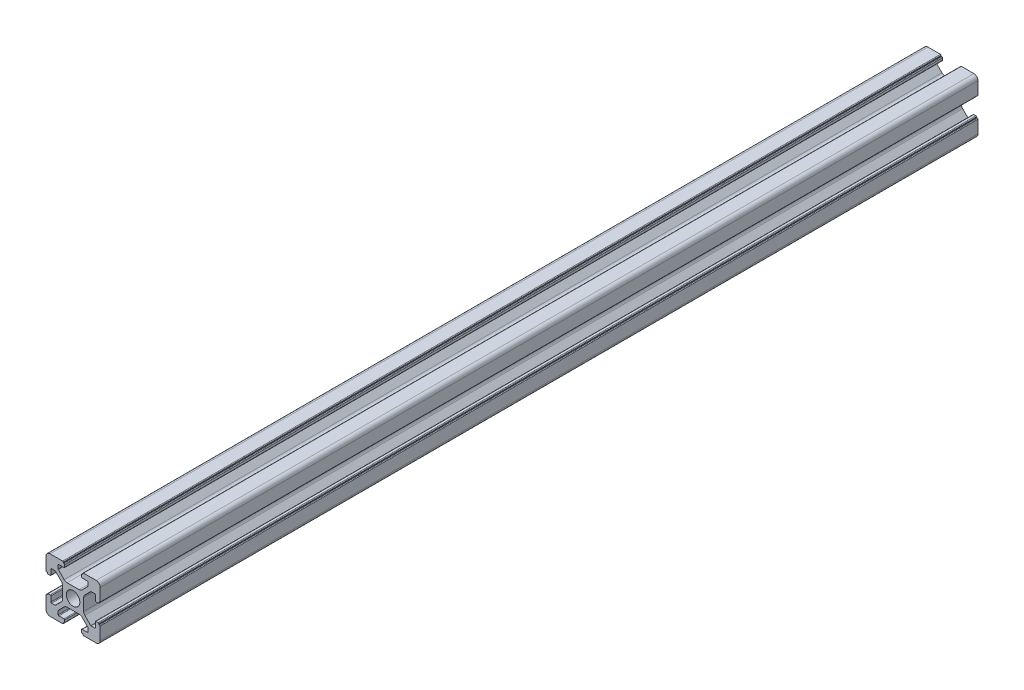
SolidWorks part; units mm, degrees
material "1060 Alloy"
ref_plane "前视基准面" through (0, 0, 0) normal (0, 0, 1) x (1, 0, 0)
ref_plane "上视基准面" through (0, 0, 0) normal (0, 1, 0) x (1, 0, 0)
ref_plane "右视基准面" through (0, 0, 0) normal (1, 0, 0) x (0, 0, -1)
sketch "草图1" plane through (0, 0, 0) normal (0, 0, 1) x (1, 0, 0)
  line L0 (0, 0) -> (0, 5.5) construction
  line L1 (-8.5023, -10.0023) -> (-3.85, -10.0023)
  line L2 (-10.0023, -8.5023) -> (-10.0023, -3.85)
  line L3 (-8.5023, 10.0023) -> (-3.85, 10.0023)
  line L4 (10.0023, -8.5023) -> (10.0023, -3.85)
  line L5 (-10.0023, -10.0023) -> (10.0023, 10.0023) construction
  line L6 (-10.0023, 10.0023) -> (10.0023, -10.0023) construction
  line L7 (-2.218, -3.9) -> (2.218, -3.9)
  line L8 (-3.9, -2.218) -> (-3.9, 2.218)
  line L9 (-2.218, 3.9) -> (2.218, 3.9)
  line L10 (3.9, -2.218) -> (3.9, 2.218)
  line L11 (-3.9, -3.9) -> (3.9, 3.9) construction
  line L12 (-3.9, 3.9) -> (3.9, -3.9) construction
  line L13 (-5.25, -8.2) -> (-3.35, -8.2)
  line L14 (-8.2, -5.25) -> (-8.2, -3.35)
  line L15 (-5.25, 8.2) -> (-3.35, 8.2)
  line L16 (8.2, -5.25) -> (8.2, -3.35)
  line L17 (-8.2, -8.2) -> (8.2, 8.2) construction
  line L18 (-8.2, 8.2) -> (8.2, -8.2) construction
  line L19 (-7.95, 5.5) -> (-6.6642, 5.5)
  line L20 (0, 0) -> (5.5, 0) construction
  line L23 (-5.5, 7.95) -> (-5.5, 6.6642)
  line L26 (0, 0) -> (-0.5303, 0.5303)
  line L27 (3.2787, 4.3393) -> (5.4268, 6.4874)
  line L28 (0, 0) -> (0.5303, -0.5303)
  line L29 (5.5, 6.6642) -> (5.5, 7.95)
  line L30 (4.3393, 3.2787) -> (6.4874, 5.4268)
  line L31 (6.6642, 5.5) -> (7.95, 5.5)
  line L32 (4.3393, -3.2787) -> (6.4874, -5.4268)
  line L33 (3.2787, -4.3393) -> (5.4268, -6.4874)
  line L34 (-3.2787, -4.3393) -> (-5.4268, -6.4874)
  line L35 (-4.3393, -3.2787) -> (-6.4874, -5.4268)
  line L36 (-4.3393, 3.2787) -> (-6.4874, 5.4268)
  line L37 (-3.2787, 4.3393) -> (-5.4268, 6.4874)
  line L38 (3.1, -8.45) -> (3.1, -9.2523)
  line L39 (8.45, 3.1) -> (9.2523, 3.1)
  line L40 (-5.5, -6.6642) -> (-5.5, -7.95)
  line L41 (-6.6642, -5.5) -> (-7.95, -5.5)
  line L42 (5.5, -6.6642) -> (5.5, -7.95)
  line L43 (6.6642, -5.5) -> (7.95, -5.5)
  line L44 (9.2523, -3.1) -> (8.45, -3.1)
  line L46 (10.0023, 3.85) -> (10.0023, 8.5023)
  line L47 (8.2, 3.35) -> (8.2, 5.25)
  line L48 (-3.1, -9.2523) -> (-3.1, -8.45)
  line L49 (-8.45, -3.1) -> (-9.2523, -3.1)
  line L50 (-9.2523, 3.1) -> (-8.45, 3.1)
  line L51 (-3.1, 8.45) -> (-3.1, 9.2523)
  line L52 (3.1, 9.2523) -> (3.1, 8.45)
  line L53 (3.85, 10.0023) -> (8.5023, 10.0023)
  line L54 (3.35, 8.2) -> (5.25, 8.2)
  line L55 (-10.0023, 3.85) -> (-10.0023, 8.5023)
  line L56 (-8.2, 3.35) -> (-8.2, 5.25)
  line L57 (3.35, -8.2) -> (5.25, -8.2)
  line L58 (3.85, -10.0023) -> (8.5023, -10.0023)
  line L59 (9.7523, -3.6) -> (9.5023, -3.6)
  line L61 (9.7523, 3.6) -> (9.5023, 3.6)
  line L62 (9.5023, -3.6) -> (9.5023, -3.35)
  line L63 (3.6, -9.7523) -> (3.6, -9.5023)
  line L64 (3.35, -9.5023) -> (3.6, -9.5023)
  line L65 (9.5023, 3.35) -> (9.5023, 3.6)
  line L66 (-3.6, -9.5023) -> (-3.35, -9.5023)
  line L67 (-3.6, -9.7523) -> (-3.6, -9.5023)
  line L68 (-9.7523, -3.6) -> (-9.5023, -3.6)
  line L69 (-9.5023, -3.35) -> (-9.5023, -3.6)
  line L70 (-9.5023, 3.6) -> (-9.5023, 3.35)
  line L71 (-9.7523, 3.6) -> (-9.5023, 3.6)
  line L72 (-3.6, 9.7523) -> (-3.6, 9.5023)
  line L73 (-3.35, 9.5023) -> (-3.6, 9.5023)
  line L74 (3.6, 9.5023) -> (3.35, 9.5023)
  line L75 (3.6, 9.7523) -> (3.6, 9.5023)
  circle A0 centre (0, 0) radius 2.5
  arc A1 (10.0023, 8.5023) -> (8.5023, 10.0023) centre (8.5023, 8.5023) ccw
  arc A2 (8.5023, -10.0023) -> (10.0023, -8.5023) centre (8.5023, -8.5023) ccw
  arc A3 (-10.0023, -8.5023) -> (-8.5023, -10.0023) centre (-8.5023, -8.5023) ccw
  arc A4 (-10.0023, 8.5023) -> (-8.5023, 10.0023) centre (-8.5023, 8.5023) cw
  arc A5 (-9.5023, -3.35) -> (-9.2523, -3.1) centre (-9.2523, -3.35) cw
  arc A6 (-9.7523, -3.6) -> (-10.0023, -3.85) centre (-9.7523, -3.85) ccw
  arc A7 (-8.45, -3.1) -> (-8.2, -3.35) centre (-8.45, -3.35) cw
  arc A8 (-7.95, -5.5) -> (-8.2, -5.25) centre (-7.95, -5.25) cw
  arc A9 (-6.4874, -5.4268) -> (-6.6642, -5.5) centre (-6.6642, -5.25) cw
  arc A10 (-5.4268, -6.4874) -> (-5.5, -6.6642) centre (-5.25, -6.6642) ccw
  arc A11 (-5.5, -7.95) -> (-5.25, -8.2) centre (-5.25, -7.95) ccw
  arc A12 (-3.6, -9.7523) -> (-3.85, -10.0023) centre (-3.85, -9.7523) cw
  arc A13 (-3.35, -9.5023) -> (-3.1, -9.2523) centre (-3.35, -9.2523) ccw
  arc A14 (-3.1, -8.45) -> (-3.35, -8.2) centre (-3.35, -8.45) ccw
  arc A15 (3.1, -8.45) -> (3.35, -8.2) centre (3.35, -8.45) cw
  arc A16 (5.5, -7.95) -> (5.25, -8.2) centre (5.25, -7.95) cw
  arc A17 (5.4268, -6.4874) -> (5.5, -6.6642) centre (5.25, -6.6642) cw
  arc A18 (6.4874, -5.4268) -> (6.6642, -5.5) centre (6.6642, -5.25) ccw
  arc A19 (7.95, -5.5) -> (8.2, -5.25) centre (7.95, -5.25) ccw
  arc A20 (8.45, -3.1) -> (8.2, -3.35) centre (8.45, -3.35) ccw
  arc A21 (9.5023, -3.35) -> (9.2523, -3.1) centre (9.2523, -3.35) ccw
  arc A22 (9.7523, -3.6) -> (10.0023, -3.85) centre (9.7523, -3.85) cw
  arc A23 (3.35, -9.5023) -> (3.1, -9.2523) centre (3.35, -9.2523) cw
  arc A24 (3.6, -9.7523) -> (3.85, -10.0023) centre (3.85, -9.7523) ccw
  arc A25 (7.95, 5.5) -> (8.2, 5.25) centre (7.95, 5.25) cw
  arc A26 (8.2, 3.35) -> (8.45, 3.1) centre (8.45, 3.35) ccw
  arc A27 (9.5023, 3.35) -> (9.2523, 3.1) centre (9.2523, 3.35) cw
  arc A28 (9.7523, 3.6) -> (10.0023, 3.85) centre (9.7523, 3.85) ccw
  arc A29 (6.6642, 5.5) -> (6.4874, 5.4268) centre (6.6642, 5.25) ccw
  arc A30 (5.4268, 6.4874) -> (5.5, 6.6642) centre (5.25, 6.6642) ccw
  arc A31 (5.5, 7.95) -> (5.25, 8.2) centre (5.25, 7.95) ccw
  arc A32 (3.1, 8.45) -> (3.35, 8.2) centre (3.35, 8.45) ccw
  arc A33 (3.6, 9.7523) -> (3.85, 10.0023) centre (3.85, 9.7523) cw
  arc A34 (3.35, 9.5023) -> (3.1, 9.2523) centre (3.35, 9.2523) ccw
  arc A35 (-9.7523, 3.6) -> (-10.0023, 3.85) centre (-9.7523, 3.85) cw
  arc A36 (-9.5023, 3.35) -> (-9.2523, 3.1) centre (-9.2523, 3.35) ccw
  arc A37 (-8.45, 3.1) -> (-8.2, 3.35) centre (-8.45, 3.35) ccw
  arc A38 (-8.2, 5.25) -> (-7.95, 5.5) centre (-7.95, 5.25) cw
  arc A39 (-6.4874, 5.4268) -> (-6.6642, 5.5) centre (-6.6642, 5.25) ccw
  arc A40 (-5.4268, 6.4874) -> (-5.5, 6.6642) centre (-5.25, 6.6642) cw
  arc A41 (-5.5, 7.95) -> (-5.25, 8.2) centre (-5.25, 7.95) cw
  arc A42 (-3.1, 8.45) -> (-3.35, 8.2) centre (-3.35, 8.45) cw
  arc A43 (-3.1, 9.2523) -> (-3.35, 9.5023) centre (-3.35, 9.2523) ccw
  arc A44 (-3.6, 9.7523) -> (-3.85, 10.0023) centre (-3.85, 9.7523) ccw
  arc A45 (-4.3393, 3.2787) -> (-3.9, 2.218) centre (-5.4, 2.218) cw
  arc A46 (-3.2787, 4.3393) -> (-2.218, 3.9) centre (-2.218, 5.4) ccw
  arc A47 (3.2787, 4.3393) -> (2.218, 3.9) centre (2.218, 5.4) cw
  arc A48 (4.3393, 3.2787) -> (3.9, 2.218) centre (5.4, 2.218) ccw
  arc A49 (4.3393, -3.2787) -> (3.9, -2.218) centre (5.4, -2.218) cw
  arc A50 (3.2787, -4.3393) -> (2.218, -3.9) centre (2.218, -5.4) ccw
  arc A51 (-4.3393, -3.2787) -> (-3.9, -2.218) centre (-5.4, -2.218) ccw
  arc A52 (-2.218, -3.9) -> (-3.2787, -4.3393) centre (-2.218, -5.4) ccw
  point P0 (0, 0)
  point P7 (10.0023, 0)
  point P62 (0, 0)
  point P76 (0, 0)
  point P92 (-8.2, -5.5)
  point P99 (0, 0)
  point P106 (-5.5, -8.2)
  point P117 (5.5, -8.2)
  point P124 (8.2, -5.5)
  point P137 (8.2, 5.5)
  point P140 (8.2, 3.1)
  point P147 (6.5607, 5.5)
  point P152 (5.5, 8.2)
  point P167 (-8.2, 5.5)
  point P174 (-5.5, 8.2)
  dimension "D1" = 1.5
  dimension "D5" = 0.25
  dimension "D6" = 1.5
  dimension "D2" = 4
  dimension "D3" = 4
  dimension "D4" = 4
extrude "凸台-拉伸1" add sketch "草图1" along normal blind 324 contours A52 L7 A50 L33 A17 L42 A16 L57 A15 L38 A23 L64 L63 A24 L58 A2 L4 A22 L59 L62 A21 L44 A20 L16 A19 L43 A18 L32 A49 L10 A48 L30 A29 L31 A25 L47 A26 L39 A27 L65 L61 A28 L46 A1 L53 A33 L75 L74 A34 L52 A32
ref_plane "Plane1" through (0, 0, 162) normal (0, 0, -1) x (-1, 0, 0)
ref_plane "Plane2" through (0, 0, 105) normal (0, 0, -1) x (-1, 0, 0)
